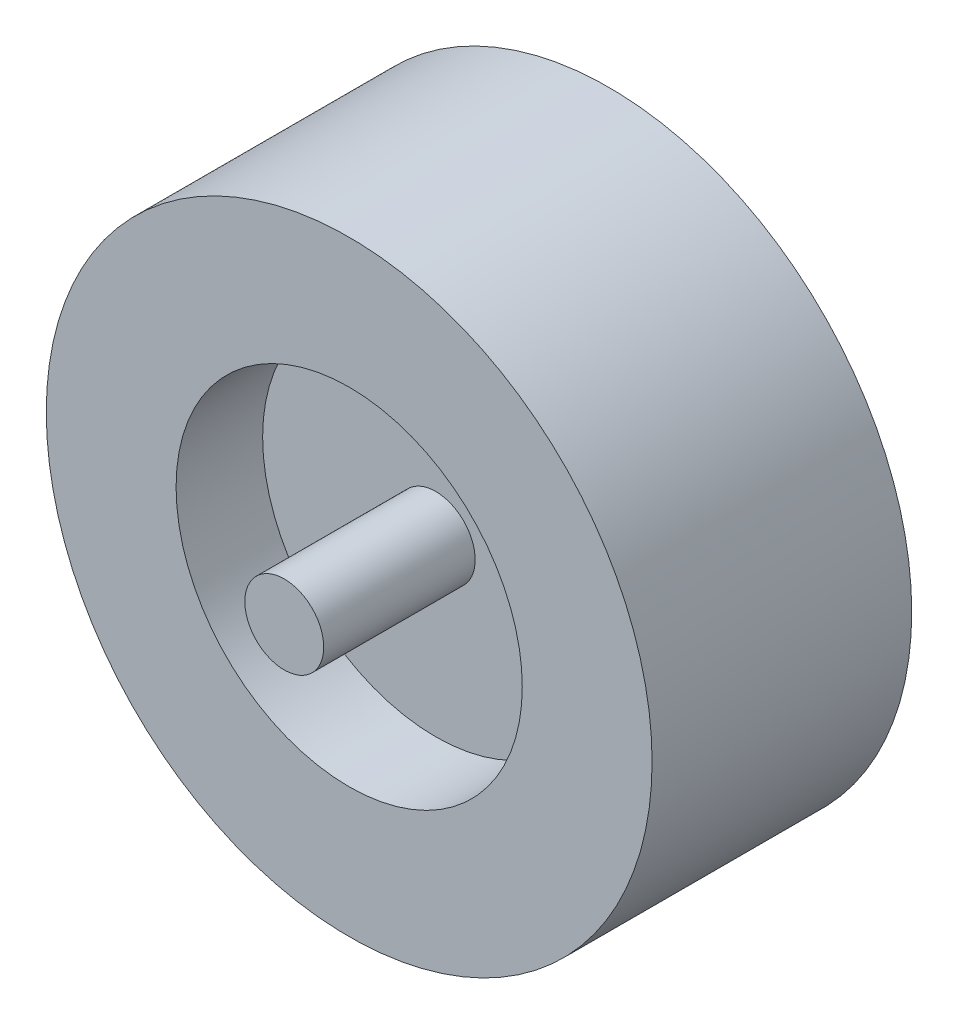
SolidWorks part; units mm, degrees
ref_plane "Front Plane" through (0, 0, 0) normal (0, 0, 1) x (1, 0, 0)
ref_plane "Top Plane" through (0, 0, 0) normal (0, 1, 0) x (1, 0, 0)
ref_plane "Right Plane" through (0, 0, 0) normal (1, 0, 0) x (0, 0, -1)
sketch "Sketch1" plane through (0, 0, 0) normal (1, 0, 0) x (0, 0, -1)
  line L1 (-57.15, 76.2) -> (-57.15, 133.35)
  line L10 (-19.05, 0) -> (19.05, 0)
  line L11 (55, 0) -> (-55, 0) construction
  line L12 (19.05, 0) -> (19.05, 76.2)
  line L13 (19.05, 76.2) -> (57.15, 76.2)
  line L14 (57.15, 76.2) -> (57.15, 133.35)
  line L15 (57.15, 133.35) -> (-57.15, 133.35)
  line L16 (0, 55) -> (0, -55) construction
  line L17 (-19.05, 76.2) -> (-57.15, 76.2)
  line L18 (-19.05, 0) -> (-19.05, 76.2)
  point P5 (0, 133.35)
  point P15 (0, 0)
  dimension "D1" = 57.15
  dimension "D2" = 133.35
  dimension "D3" = 76.2
  dimension "D4" = 38.1
revolve "Revolve1" add sketch "Sketch1" angle 360 about L10
sketch "Sketch4" plane through (0, 0, 0) normal (0, 0, -1) x (-1, 0, 0)
  circle A0 centre (0, 0) radius 17.3672
  dimension "D1" = 34.7345
extrude "Boss-Extrude1" add sketch "Sketch4" along normal mid plane 171.45
